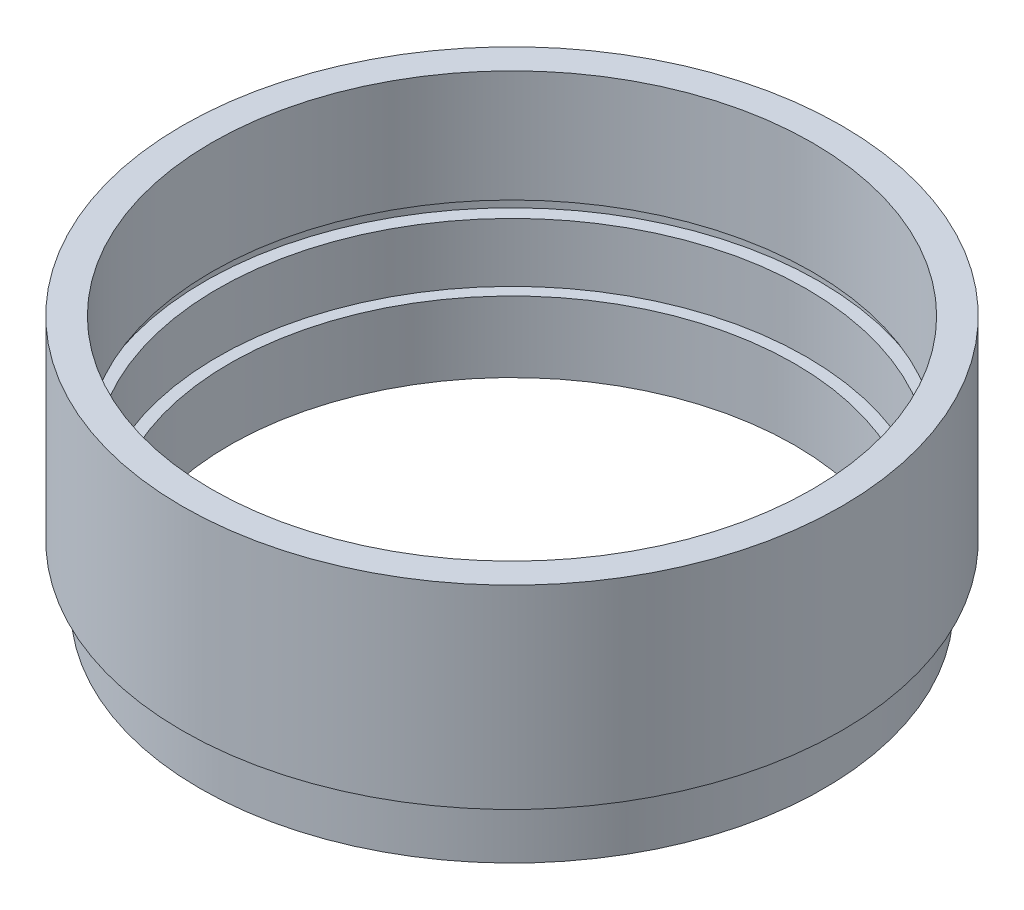
SolidWorks part; units mm, degrees
ref_plane "前视基准面" through (0, 0, 0) normal (0, 0, 1) x (1, 0, 0)
ref_plane "上视基准面" through (0, 0, 0) normal (0, 1, 0) x (1, 0, 0)
ref_plane "右视基准面" through (0, 0, 0) normal (1, 0, 0) x (0, 0, -1)
sketch "草图1" plane through (0, 0, 0) normal (0, 0, 1) x (1, 0, 0)
  line L0 (0, 0) -> (0, 21.8535) construction
  line L1 (24, 0) -> (26.5, 0)
  line L2 (26.5, 0) -> (26.5, 4)
  line L3 (26.5, 4) -> (25.5, 4)
  line L4 (25.5, 4) -> (25.5, 5)
  line L5 (25.5, 5) -> (28, 5)
  line L6 (28, 5) -> (28, 21.5)
  line L7 (28, 21.5) -> (25.5, 21.5)
  line L8 (25.5, 21.5) -> (25.5, 12)
  line L9 (25.5, 12) -> (26.1, 12)
  line L10 (26.1, 12) -> (26.1, 11)
  line L11 (26.1, 11) -> (25, 11)
  line L12 (25, 11) -> (25, 6)
  line L13 (25, 6) -> (24, 6)
  line L14 (24, 0) -> (24, 6)
  dimension "D1" = 21.5
  dimension "D2" = 28
  dimension "D3" = 25.5
  dimension "D4" = 25
  dimension "D5" = 1
  dimension "D6" = 5
  dimension "D7" = 24
  dimension "D8" = 26.5
  dimension "D9" = 1
  dimension "D10" = 5
  dimension "D11" = 6
  dimension "D12" = 26.1
  dimension "D13" = 25.5
revolve "旋转1" add sketch "草图1" angle 360 about L0
cosmetic thread "装饰螺纹线11"
cosmetic thread "装饰螺纹线12"
